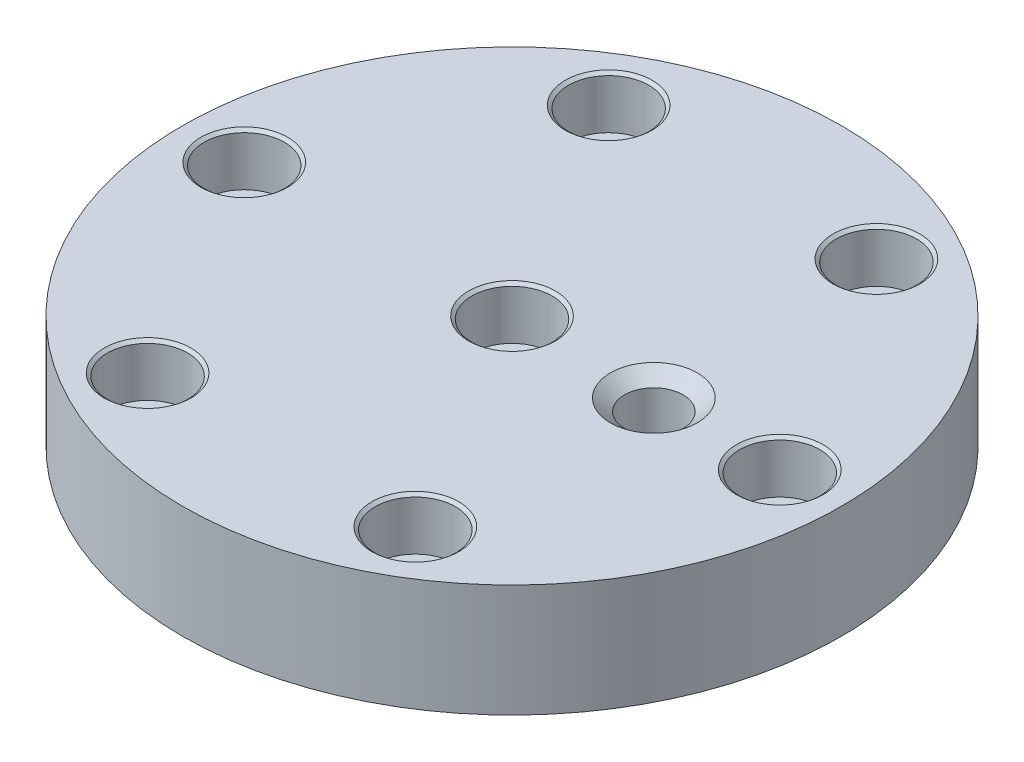
SolidWorks part; units mm, degrees
ref_plane "Front Plane" through (0, 0, 0) normal (0, 0, 1) x (1, 0, 0)
ref_plane "Top Plane" through (0, 0, 0) normal (0, 1, 0) x (1, 0, 0)
ref_plane "Right Plane" through (0, 0, 0) normal (1, 0, 0) x (0, 0, -1)
sketch "Sketch1" plane through (0, 0, 0) normal (0, 1, 0) x (1, 0, 0)
  circle A0 centre (0, 0) radius 79
  circle A1 centre (0, 0) radius 6
  dimension "D1" = 12
extrude "Boss-Extrude1" add sketch "Sketch1" along normal blind 27
hole_wizard "CBORE for #0 Binding Head Machine Screw1" positions "Sketch4" profile "Sketch5" counterbore size "#0" standard "ANSI Inch" end condition through all
sketch "Sketch4" plane through (0, 27, 0) normal (0, 1, 0) x (1, 0, 0)
  line L0 (0, 0) -> (32, 55.4256) construction
  circle A1 centre (0, 0) radius 64 construction
  point P0 (31.8386, 55.5185)
  point P19 (63.9997, 0.1862)
  point P20 (32.1612, -55.3323)
  point P21 (-31.8386, -55.5185)
  point P22 (-63.9997, -0.1862)
  point P23 (-32.1612, 55.3323)
  point P24 (0, 0)
  dimension "D1" = 6
sketch "Sketch5" plane through (31.8386, 27, -55.5185) normal (1, 0, 0) x (0, 0, 1)
  line L0 (0, 0) -> (0, 27)
  line L1 (0, 27) -> (6.25, 27)
  line L3 (6.25, 27) -> (6.25, 12.5)
  line L4 (9.625, 12.5) -> (6.25, 12.5)
  line L5 (9.625, 12.5) -> (9.625, 0.6514)
  line L6 (9.625, 0.6514) -> (10.4013, 0)
  line L7 (10.4013, 0) -> (0, 0)
  line L8 (-9.625, 0.6514) -> (-10.4013, 0) construction
  line L11 (0, -6.35) -> (0, 107.95) construction
  dimension "Thru Hole Dia." = 12.5
  dimension "Thru Hole Depth" = 27
  dimension "C'Bore Dia." = 19.25
  dimension "C'Bore Depth" = 12.5
  dimension "Near C'Sink Dia." = 20.8026
  dimension "Near C'Sink Angle" = 100
hole_wizard "#97 (0.0059) Diameter Hole1" positions "Sketch8" profile "Sketch9" hole size "#97" standard "ANSI Inch"
sketch "Sketch8" plane through (0, 27, 0) normal (0, 1, 0) x (1, 0, 0)
  line L0 (-14.85, 0) -> (14.85, 0) construction
  point P0 (34, 0)
  dimension "D1" = 34
sketch "Sketch9" plane through (34, 27, 0) normal (1, 0, 0) x (0, 0, 1)
  line L0 (0, 0) -> (0, 21.206)
  line L1 (0, 21.206) -> (7, 17)
  line L2 (7, 17) -> (7, 2.854)
  line L3 (7, 2.854) -> (10.4013, 0)
  line L5 (10.4013, 0) -> (0, 0)
  line L6 (-7, 2.854) -> (-10.4013, 0) construction
  line L10 (0, 21.206) -> (-7, 17) construction
  line L11 (0, -6.35) -> (0, 107.95) construction
  dimension "Hole Dia." = 14
  dimension "Hole Depth" = 17
  dimension "Near C'Sink Dia." = 20.8026
  dimension "Near C'Sink Angle" = 100
  dimension "Drill Angle" = 118
